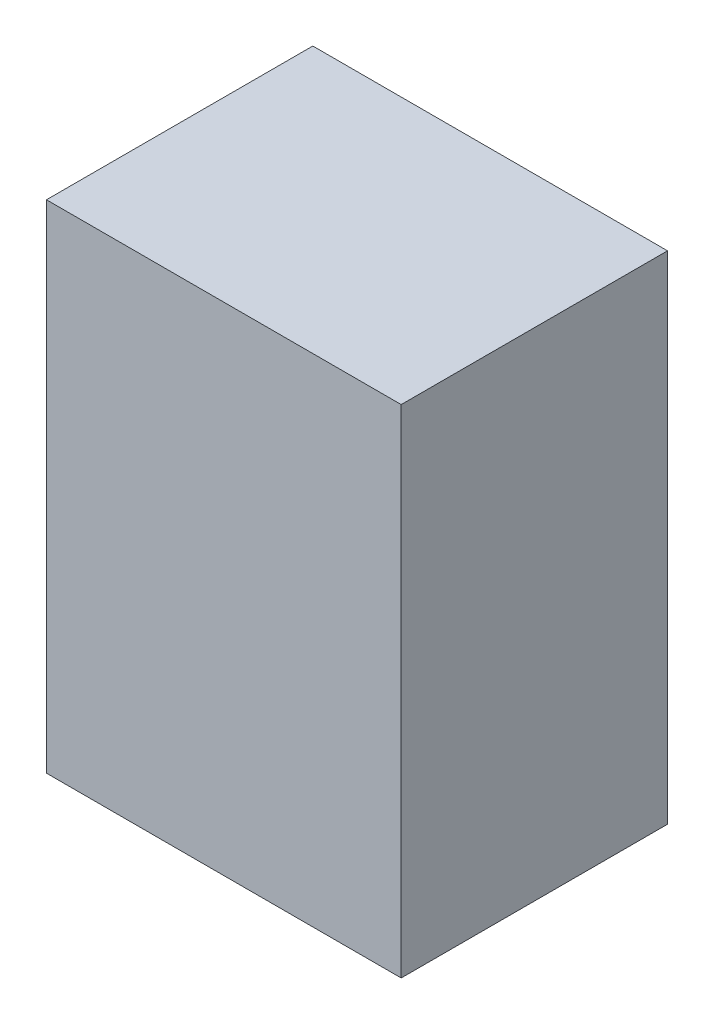
SolidWorks part; units mm, degrees
ref_plane "前视基准面" through (0, 0, 0) normal (0, 0, 1) x (1, 0, 0)
ref_plane "上视基准面" through (0, 0, 0) normal (0, 1, 0) x (1, 0, 0)
ref_plane "右视基准面" through (0, 0, 0) normal (1, 0, 0) x (0, 0, -1)
sketch "草图1" plane through (0, 0, 0) normal (0, 0, 1) x (1, 0, 0)
  line L1 (-12.5, -17.5) -> (12.5, -17.5)
  line L2 (-12.5, -17.5) -> (-12.5, 17.5)
  line L3 (-12.5, 17.5) -> (12.5, 17.5)
  line L4 (12.5, -17.5) -> (12.5, 17.5)
  line L5 (-12.5, -17.5) -> (12.5, 17.5) construction
  line L6 (-12.5, 17.5) -> (12.5, -17.5) construction
  point P0 (0, 0)
  dimension "D1" = 25
  dimension "D2" = 35
extrude "凸台-拉伸1" add sketch "草图1" along normal blind 18.77
